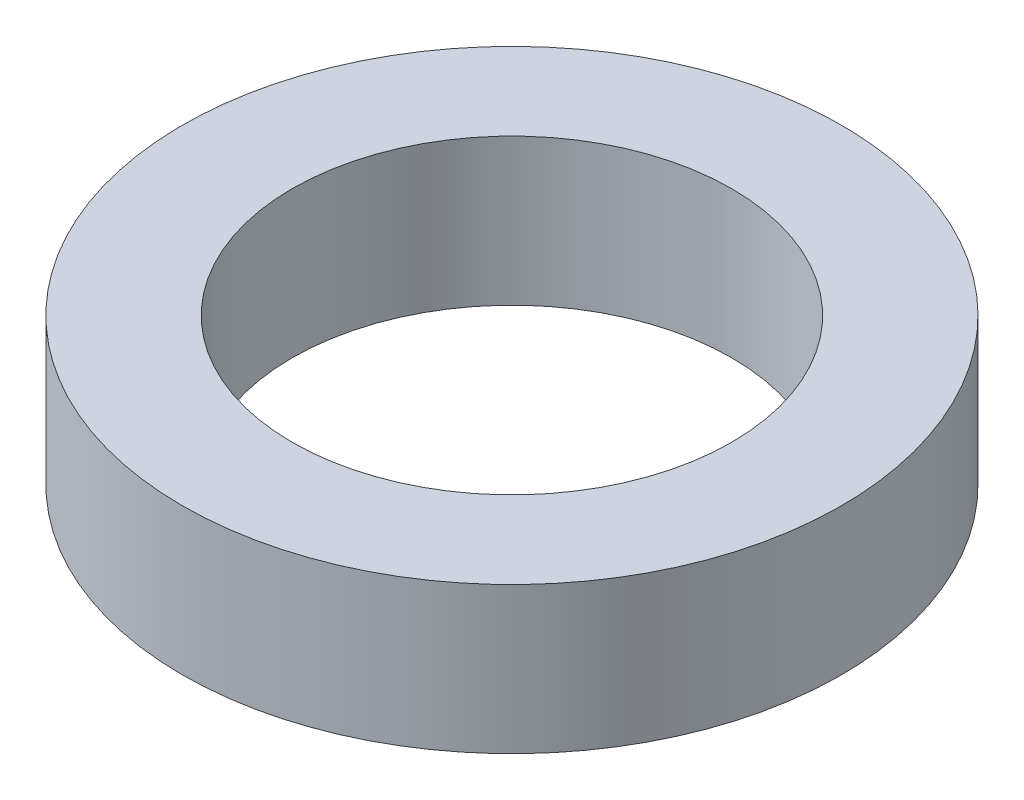
SolidWorks part; units mm, degrees
ref_plane "Front Plane" through (0, 0, 0) normal (0, 0, 1) x (1, 0, 0)
ref_plane "Top Plane" through (0, 0, 0) normal (0, 1, 0) x (1, 0, 0)
ref_plane "Right Plane" through (0, 0, 0) normal (1, 0, 0) x (0, 0, -1)
sketch "Sketch1" plane through (0, 0, 0) normal (0, 1, 0) x (1, 0, 0)
  circle A0 centre (0, 0) radius 6
  circle A1 centre (0, 0) radius 9
  dimension "D1" = 12
  dimension "D2" = 18
extrude "Boss-Extrude1" add sketch "Sketch1" along normal blind 4
